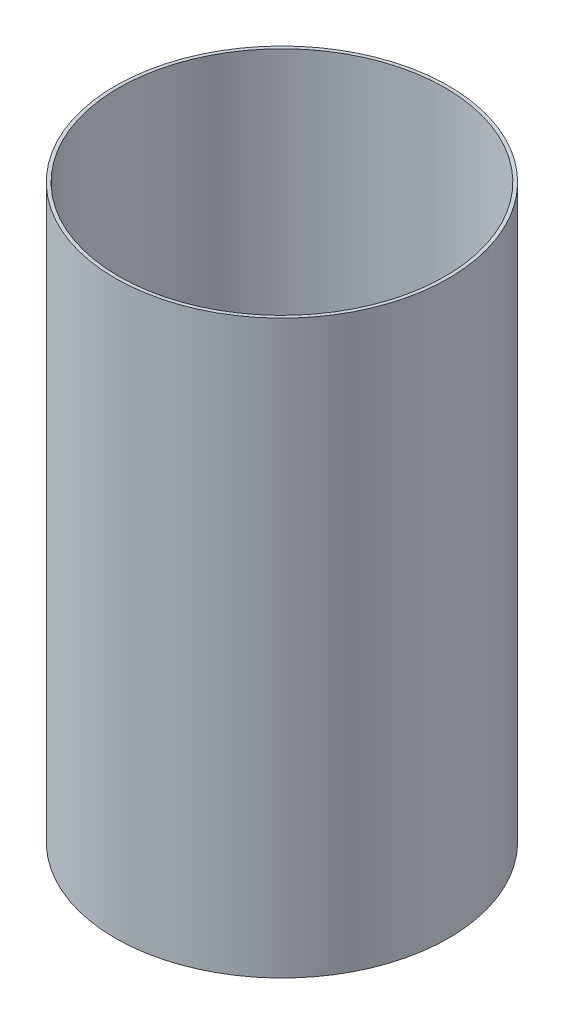
SolidWorks part; units mm, degrees
material "PTFE (general)"
ref_plane "Front Plane" through (0, 0, 0) normal (0, 0, 1) x (1, 0, 0)
ref_plane "Top Plane" through (0, 0, 0) normal (0, 1, 0) x (1, 0, 0)
ref_plane "Right Plane" through (0, 0, 0) normal (1, 0, 0) x (0, 0, -1)
ref_axis "Axis1" through (0, 55, 0) along (0, -1, 0)
sketch "Sketch2" plane through (0, 0, 0) normal (0, 0, 1) x (1, 0, 0)
  line L1 (-38.8874, 0) -> (-38.1, 0)
  line L2 (-38.8874, 0) -> (-38.8874, -133.35)
  line L3 (-38.8874, -133.35) -> (-38.1, -133.35)
  line L4 (-38.1, 0) -> (-38.1, -133.35)
  dimension "D2" = 0.7874
revolve "Revolve1" add sketch "Sketch2" angle 360 about axis through (0, 55, 0) along (0, -1, 0)
equation "\"D2@Sketch2\"=\"LINER THICKNESS@Cryo Tank.Assembly\""
